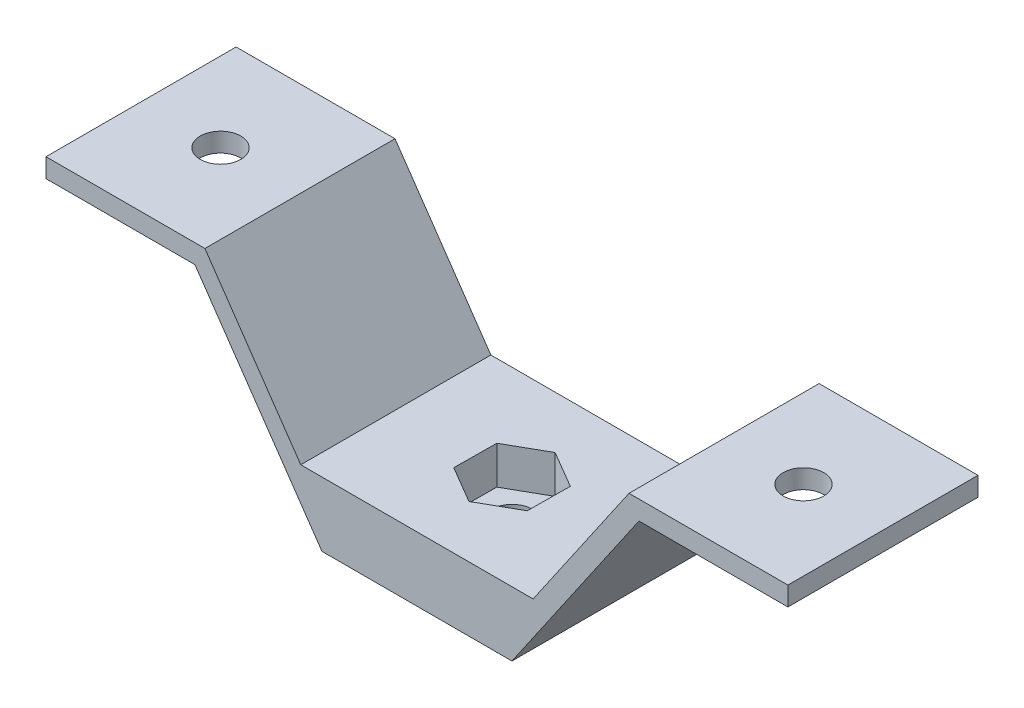
SolidWorks part; units mm, degrees
material "ABS"
ref_plane "Front Plane" through (0, 0, 0) normal (0, 0, 1) x (1, 0, 0)
ref_plane "Top Plane" through (0, 0, 0) normal (0, 1, 0) x (1, 0, 0)
ref_plane "Right Plane" through (0, 0, 0) normal (1, 0, 0) x (0, 0, -1)
sketch "Sketch1" plane through (0, 0, 0) normal (0, 0, 1) x (1, 0, 0)
  line L0 (0, 0) -> (14.9905, 0)
  line L1 (14.9905, 0) -> (35.0385, 29.16)
  line L2 (35.0385, 29.16) -> (58.5396, 29.16)
  line L3 (58.5396, 29.16) -> (58.5396, 32.16)
  line L4 (58.5396, 32.16) -> (33.4604, 32.16)
  line L5 (33.4604, 32.16) -> (18.3351, 10.16)
  line L6 (18.3351, 10.16) -> (0, 10.16)
  line L7 (46, 32.16) -> (46, 58.6255) construction
  line L8 (0, 0) -> (0, 46.6851) construction
  line L9 (0, 10.16) -> (0, 0)
  dimension "D1" = 46
  dimension "D2" = 10.16
  dimension "D3" = 22
  dimension "D4" = 3
  dimension "D5" = 3
extrude "Boss-Extrude1" add sketch "Sketch1" against normal blind 30
mirror "Mirror1" about plane through (0, 10.16, -30) normal (-1, 0, 0) of "Boss-Extrude1"
sketch "Sketch2" plane through (0, 32.16, 0) normal (0, 1, 0) x (1, 0, 0)
  line L0 (0, -16.5) -> (0, 16.5) construction
  line L1 (-58.5396, 0) -> (-33.4604, 0) construction
  circle A0 centre (-46, 15) radius 3.2
  dimension "D1" = 6.4
  dimension "D2" = 46
  dimension "D3" = 15
extrude "Cut-Extrude1" cut sketch "Sketch2" against normal up to next (3 mm away)
mirror "Mirror2" about plane through (0, 0, 0) normal (1, 0, 0) of "Cut-Extrude1"
sketch "Sketch4" plane through (0, 32.16, 0) normal (0, 1, 0) x (1, 0, 0)
  line L0 (46, 15) -> (-45.9877, 15) construction
sketch "Sketch5" plane through (0, 10.16, 0) normal (0, 1, 0) x (1, 0, 0)
  line L0 (46, 15) -> (-45.9877, 15) construction
  circle A0 centre (0.0061, 15) radius 3.2
  dimension "D1" = 6.4
extrude "Cut-Extrude2" cut sketch "Sketch5" against normal up to next
sketch "Sketch6" plane through (0, 10.16, 0) normal (0, 1, 0) x (1, 0, 0)
  line L0 (46, 15) -> (-45.9877, 15) construction
  line L1 (-5.8095, 18.4182) -> (-5.8619, 11.6727)
  line L2 (-5.8619, 11.6727) -> (-0.0463, 8.2544)
  line L3 (-0.0463, 8.2544) -> (5.8217, 11.5818)
  line L4 (5.8217, 11.5818) -> (5.8742, 18.3273)
  line L5 (5.8742, 18.3273) -> (0.0586, 21.7456)
  line L6 (0.0586, 21.7456) -> (-5.8095, 18.4182)
  circle A0 centre (0.0061, 15) radius 5.842 construction
  dimension "D1" = 11.684
extrude "Cut-Extrude3" cut sketch "Sketch6" against normal blind 6
